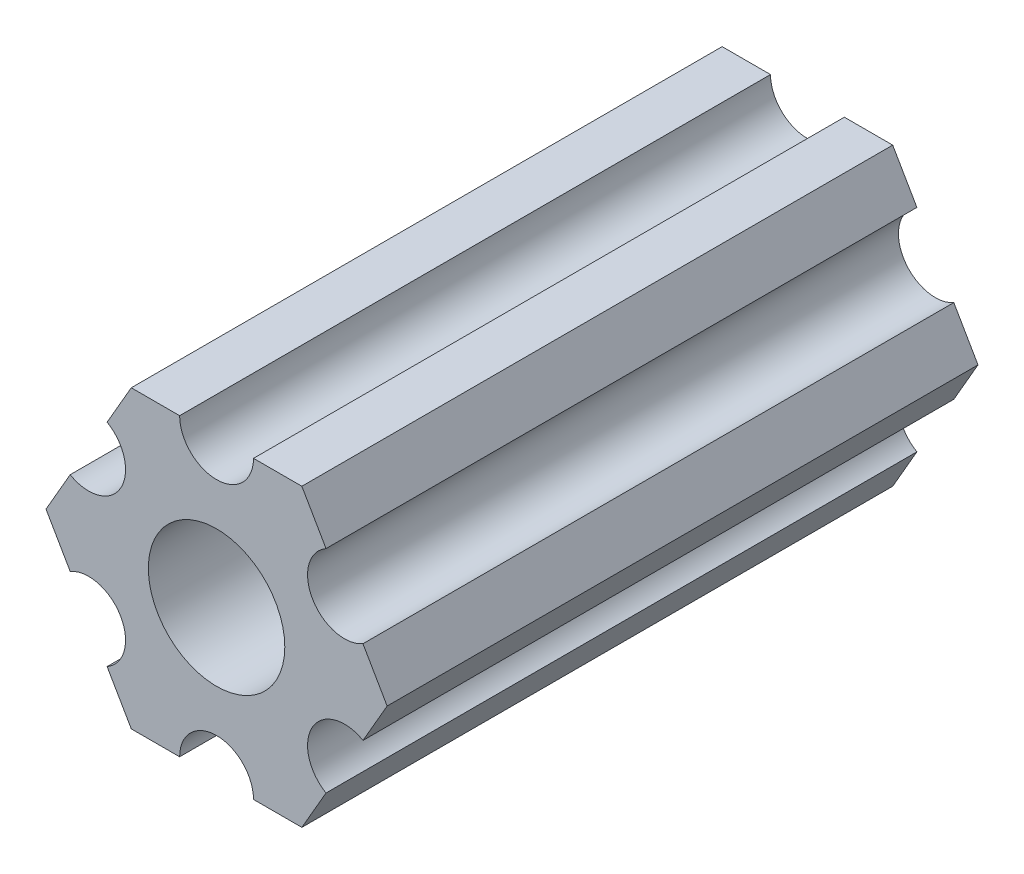
SolidWorks part; units mm, degrees
material "6005A-T61 Aluminum"
ref_plane "Front Plane" through (0, 0, 0) normal (0, 0, 1) x (1, 0, 0)
ref_plane "Top Plane" through (0, 0, 0) normal (0, 1, 0) x (1, 0, 0)
ref_plane "Right Plane" through (0, 0, 0) normal (1, 0, 0) x (0, 0, -1)
sketch "Sketch1" plane through (0, 0, 0) normal (0, 0, 1) x (1, 0, 0)
  line L0 (-4.7055, -4.5498) -> (-3.6662, -6.35)
  line L1 (3.6662, 6.35) -> (1.5875, 6.35)
  line L2 (-3.6662, 6.35) -> (-4.7055, 4.5498)
  line L3 (-7.3323, 0) -> (-6.293, -1.8002)
  line L4 (-3.6662, -6.35) -> (-1.5875, -6.35)
  line L5 (3.6662, -6.35) -> (4.7055, -4.5498)
  line L6 (7.3323, 0) -> (6.293, 1.8002)
  line L7 (1.5875, -6.35) -> (3.6662, -6.35)
  line L8 (6.293, -1.8002) -> (7.3323, 0)
  line L9 (4.7055, 4.5498) -> (3.6662, 6.35)
  line L10 (-1.5875, 6.35) -> (-3.6662, 6.35)
  line L11 (-6.293, 1.8002) -> (-7.3323, 0)
  arc A0 (-4.5399, -4.4398) -> (-1.575, -6.1516) centre (0, 0) ccw construction
  circle A1 centre (0, 0) radius 2.9337
  arc A2 (-1.5875, 6.35) -> (1.5875, 6.35) centre (0, 6.35) ccw
  arc A3 (4.7055, 4.5498) -> (6.293, 1.8002) centre (5.4993, 3.175) ccw
  arc A4 (6.293, -1.8002) -> (4.7055, -4.5498) centre (5.4993, -3.175) ccw
  arc A5 (1.5875, -6.35) -> (-1.5875, -6.35) centre (0, -6.35) ccw
  arc A6 (-4.7055, -4.5498) -> (-6.293, -1.8002) centre (-5.4993, -3.175) ccw
  arc A7 (-6.293, 1.8002) -> (-4.7055, 4.5498) centre (-5.4993, 3.175) ccw
  arc A8 (1.575, -6.1516) -> (4.5399, -4.4398) centre (0, 0) ccw construction
  arc A9 (6.1149, -1.7117) -> (6.1149, 1.7117) centre (0, 0) ccw construction
  arc A10 (4.5399, 4.4398) -> (1.575, 6.1516) centre (0, 0) ccw construction
  arc A11 (-1.575, 6.1516) -> (-4.5399, 4.4398) centre (0, 0) ccw construction
  arc A12 (-6.1149, 1.7117) -> (-6.1149, -1.7117) centre (0, 0) ccw construction
  point P24 (0, 0)
  dimension "D2" = 5.8674
  dimension "D3" = 3.175
  dimension "D1" = 12.7
  dimension "D4" = 6
extrude "Boss-Extrude1" add sketch "Sketch1" against normal blind 25.4
equation "\"Length\" = 1"
equation "\"D1@Boss-Extrude1\"=\"Length\""
